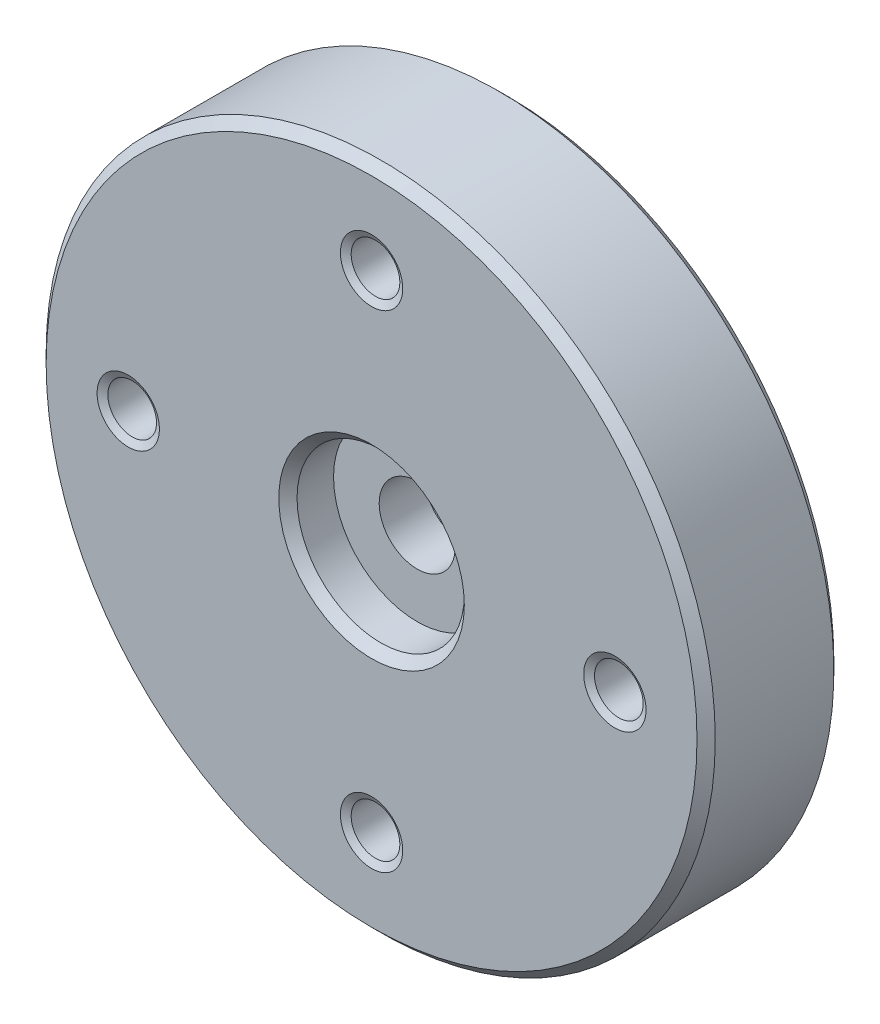
SolidWorks part; units mm, degrees
ref_plane "Front" through (0, 0, 0) normal (0, 0, 1) x (1, 0, 0)
ref_plane "Top" through (0, 0, 0) normal (0, 1, 0) x (1, 0, 0)
ref_plane "Right" through (0, 0, 0) normal (1, 0, 0) x (0, 0, -1)
sketch "Sketch1" plane through (0, 0, 0) normal (1, 0, 0) x (0, 0, -1)
  line L0 (0, 0) -> (-91.1734, 0) construction
  line L1 (3, 1.25) -> (1.5, 1.25)
  line L2 (0, 2.75) -> (0, 11)
  line L3 (0, 11) -> (4.5, 11)
  line L4 (4.5, 11) -> (4.5, 4.5)
  line L5 (4.5, 4.5) -> (6.7, 4.5)
  line L6 (6.7, 4.5) -> (6.7, 2.75)
  line L7 (6.7, 2.75) -> (3, 2.75)
  line L8 (3, 2.75) -> (3, 1.25)
  line L9 (0, 2.75) -> (1.5, 2.75)
  line L10 (1.5, 2.75) -> (1.5, 1.25)
revolve "Revolve1" add sketch "Sketch1" angle 360 about L0
hole_wizard "M2 Tapped Hole1" positions "Sketch3" profile "Sketch4"
sketch "Sketch3" plane through (0, 0, 0) normal (0, 0, 1) x (1, 0, 0)
  circle A0 centre (0, 0) radius 8 construction
  point P0 (0, 8)
  point P14 (8, 0)
  point P15 (0, -8)
  point P16 (-8, 0)
  point P17 (0, 0)
sketch "Sketch4" plane through (0, 8, 0) normal (1, 0, 0) x (0, -1, 0)
  line L0 (0, 0) -> (0, 4.5)
  line L1 (0, 4.5) -> (1.025, 4.5)
  line L2 (0.8, 4.3701) -> (0.8, 0.1299)
  line L3 (0.8, 0.1299) -> (1.025, 0)
  line L5 (1.025, 0) -> (0, 0)
  line L6 (-0.8, 0.1299) -> (-1.025, 0) construction
  line L7 (1.025, 4.5) -> (0.8, 4.3701)
  line L8 (-1.025, 4.5) -> (-0.8, 4.3701) construction
  line L11 (0, -6.35) -> (0, 107.95) construction
cosmetic thread "Hole Thread1"
cosmetic thread "Hole Thread2"
cosmetic thread "Hole Thread3"
cosmetic thread "Hole Thread4"
chamfer "Chamfer1" distance 0.3 angle 45 4 edges at (-11, 0, -4.5) (-11, 0, 0) (-4.5, 0, -6.7) (-2.75, 0, 0)
